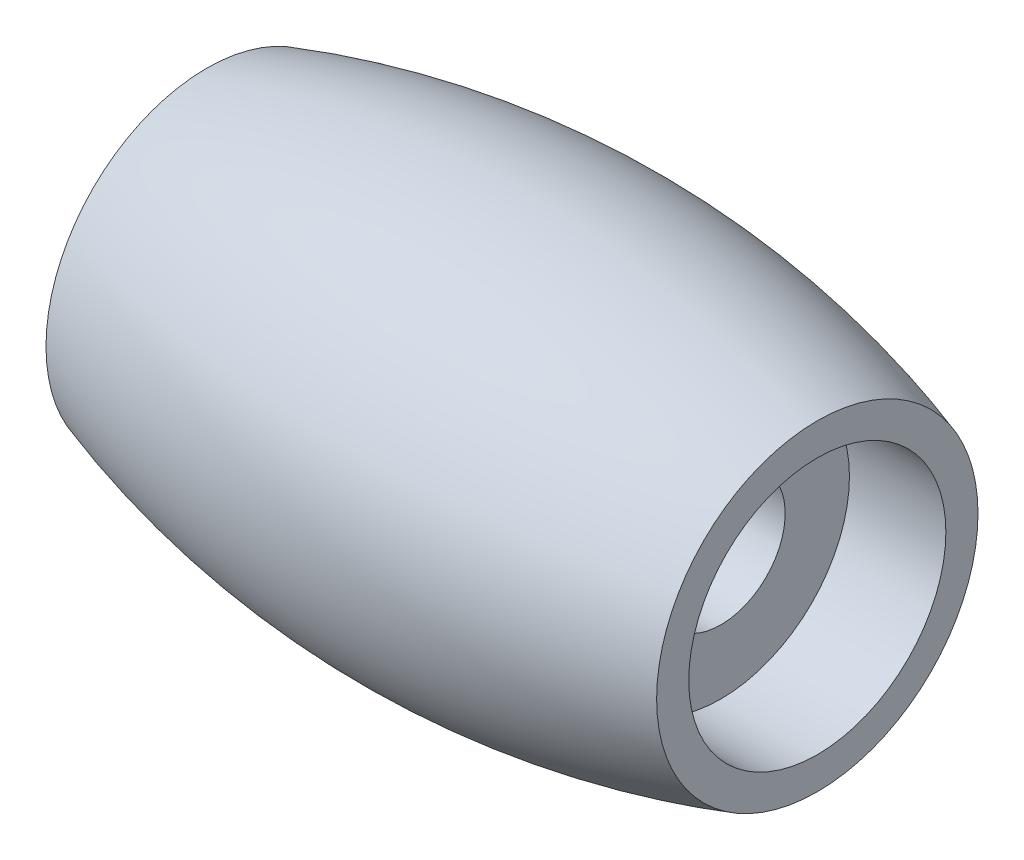
SolidWorks part; units mm, degrees
ref_plane "Front Plane" through (0, 0, 0) normal (0, 0, 1) x (1, 0, 0)
ref_plane "Top Plane" through (0, 0, 0) normal (0, 1, 0) x (1, 0, 0)
ref_plane "Right Plane" through (0, 0, 0) normal (1, 0, 0) x (0, 0, -1)
sketch "Sketch1" plane through (0, 0, 0) normal (0, 0, 1) x (1, 0, 0)
  line L0 (0, 0) -> (20.3808, 0) construction
  line L1 (0, 4) -> (0, 5)
  line L2 (0, 4) -> (3, 4)
  line L3 (3, 4) -> (3, 2)
  line L4 (3, 2) -> (16, 2)
  line L5 (16, 2) -> (16, 4)
  line L6 (16, 4) -> (19, 4)
  line L7 (19, 4) -> (19, 5)
  arc A0 (0, 5) -> (19, 5) centre (9.5, -24.333) cw
  point P13 (9.5, 6.5)
  dimension "D5" = 30.833
  dimension "D1" = 19
  dimension "D2" = 3
  dimension "D3" = 8
  dimension "D4" = 4
  dimension "D6" = 10
  dimension "D7" = 13
revolve "Revolve1" add sketch "Sketch1" angle 360 about L0
sketch "Sketch3" plane through (0, 0, 0) normal (0, 0, 1) x (1, 0, 0)
  line L0 (-0.9954, 0) -> (19.8894, 0) construction
  line L1 (0, 5) -> (0, 5.15)
  line L2 (9.4003, -0.6366) -> (9.4003, 7.1254) construction
  line L4 (0, 5) -> (19, 5)
  line L5 (19, 5) -> (19, 5.15)
  arc A1 (19, 5.15) -> (0, 5.15) centre (9.5, -23.8328) ccw
  point P9 (0, 0)
  point P10 (0, 0)
  dimension "D1" = 30.5
  dimension "D2" = 0.15
revolve "Revolve2" [suppressed] add sketch "Sketch3" angle 360 about L4
pattern_circular "CirPattern2" [suppressed] count 10 over 360
